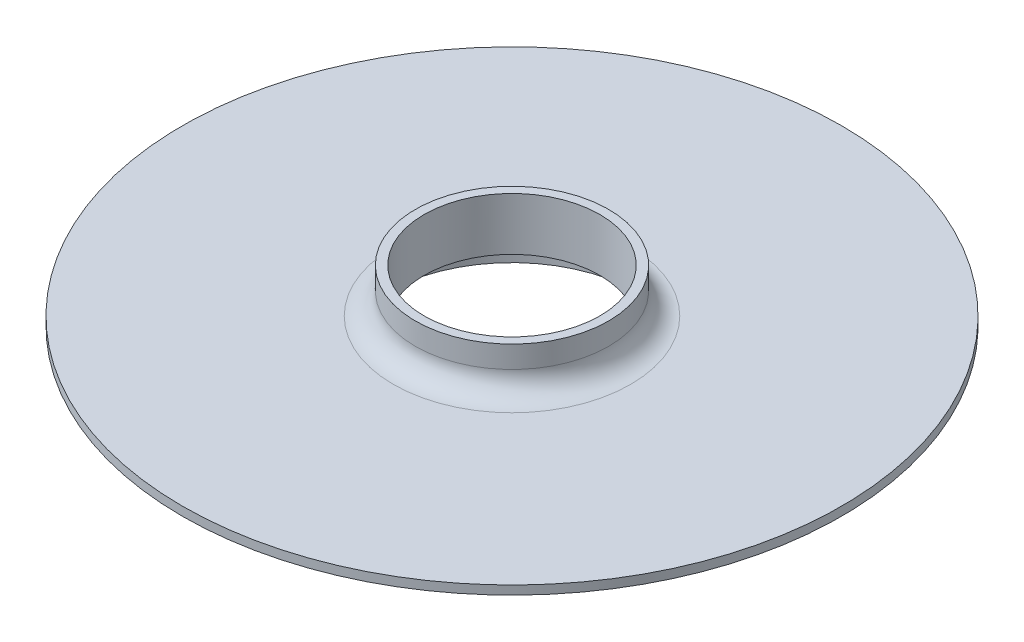
SolidWorks part; units mm, degrees
ref_plane "Front Plane" through (0, 0, 0) normal (0, 0, 1) x (1, 0, 0)
ref_plane "Top Plane" through (0, 0, 0) normal (0, 1, 0) x (1, 0, 0)
ref_plane "Right Plane" through (0, 0, 0) normal (1, 0, 0) x (0, 0, -1)
sketch "Sketch1" plane through (0, 0, 0) normal (0, 1, 0) x (1, 0, 0)
  circle A0 centre (0, 0) radius 75
  dimension "D1" = 150
extrude "Boss-Extrude1" add sketch "Sketch1" along normal blind 2
sketch "Sketch2" plane through (0, 0, 0) normal (0, -1, 0) x (1, 0, 0)
  circle A0 centre (0, 0) radius 29
  dimension "D1" = 58
extrude "Extrude-Thin1" add sketch "Sketch2" along normal blind 8 thin
sketch "Sketch3" plane through (0, 0, 0) normal (0, -1, 0) x (1, 0, 0)
  circle A0 centre (0, 0) radius 20
  dimension "D1" = 40
extrude "Cut-Extrude1" cut sketch "Sketch3" against normal through all
sketch "Sketch4" plane through (0, 2, 0) normal (0, 1, 0) x (1, 0, 0)
  circle A0 centre (0, 0) radius 20
extrude "Extrude-Thin2" add sketch "Sketch4" along normal blind 10 thin
fillet "Fillet1" radius 5 1 edges at (22, 2, 0)
